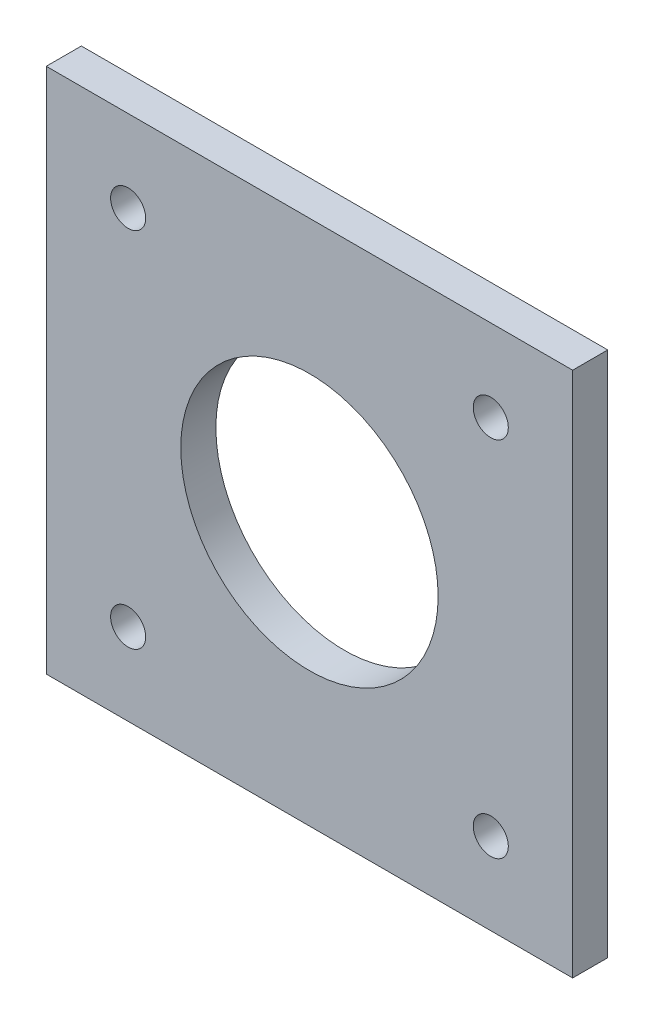
SolidWorks part; units mm, degrees
material "Plain Carbon Steel"
ref_plane "Front Plane" through (0, 0, 0) normal (0, 0, 1) x (1, 0, 0)
ref_plane "Top Plane" through (0, 0, 0) normal (0, 1, 0) x (1, 0, 0)
ref_plane "Right Plane" through (0, 0, 0) normal (1, 0, 0) x (0, 0, -1)
sketch "Sketch1" plane through (0, 0, 0) normal (0, 0, 1) x (1, 0, 0)
  line L0 (16.7358, 20.15) -> (-16.7358, 20.15)
  line L1 (-16.7358, 20.15) -> (-20.15, 16.7358)
  line L2 (-20.15, 16.0771) -> (-20.15, -16.7358)
  line L5 (-16.7358, -20.15) -> (16.7358, -20.15)
  line L7 (20.15, -16.7358) -> (20.15, 16.7358)
  line L8 (20.15, 16.7358) -> (16.7358, 20.15)
  line L9 (-20.15, 16.0771) -> (-20.15, 16.7358)
  line L10 (-20.15, -16.7358) -> (-20.15, -20.15)
  line L11 (-20.15, -20.15) -> (-16.7358, -20.15)
  line L12 (16.7358, -20.15) -> (20.15, -20.15)
  line L13 (20.15, -20.15) -> (20.15, -16.7358)
  line L15 (-22.5, 22.5) -> (22.5, 22.5)
  line L16 (-22.5, 22.5) -> (-22.5, -22.5)
  line L17 (-22.5, -22.5) -> (22.5, -22.5)
  line L18 (22.5, 22.5) -> (22.5, -22.5)
  circle A0 centre (-15.5, 15.5) radius 1.5
  circle A1 centre (-15.5, -15.5) radius 1.5
  circle A2 centre (15.5, 15.5) radius 1.5
  circle A3 centre (15.5, -15.5) radius 1.5
  circle A4 centre (0, 0) radius 11
  dimension "D1" = 22
  dimension "D2" = 3
  dimension "D3" = 3
  dimension "D4" = 3
  dimension "D5" = 3
  dimension "D6" = 45
  dimension "D7" = 45
  dimension "D8" = 22.5
  dimension "D9" = 22.5
extrude "Boss-Extrude1" add sketch "Sketch1" along normal blind 3 contours L18 L15 L16 L17 L13 L12 L5 L11 L10 L2 L9 L1 L0 L8 L7 | L12 L13 L7 L8 L0 L1 L9 L2 L10 L11 L5 A4 A3 A2 A1 A0
sketch "Sketch2" plane through (0, -24.1499, 0) normal (0, 1, 0) x (1, 0, 0)
  line L7 (6.0001, 199.3766) -> (6.0001, -250.6234) construction
  line L8 (5.9984, 199.3766) -> (5.9984, -250.6234) construction
  line L9 (-5.9999, 199.3766) -> (-5.9999, -250.6234) construction
  line L10 (-22.5, -3) -> (-22.5, 0) construction
  line L11 (5.9001, -64) -> (-5.8999, -64)
  line L12 (5.9001, -64) -> (5.9001, 1)
  line L13 (5.9001, 1) -> (-5.8999, 1)
  line L14 (-5.8999, -64) -> (-5.8999, 1)
  line L15 (-22.5, 1) -> (22.5, 1)
  line L16 (-22.5, 1) -> (-22.5, -64)
  line L19 (-19.4999, 0) -> (19.5, 0)
  line L21 (-22.5, -64) -> (22.5, -64)
  line L22 (22.5, 1) -> (22.5, -64)
  line L25 (-22.5, -3) -> (22.5, -3) construction
  line L26 (22.5, -3) -> (22.5, 0) construction
  circle A0 centre (0.0001, -34) radius 2
  circle A1 centre (-0.0016, -59) radius 2
  point P2 (22.5, -1.5)
  dimension "D3" = 4
  dimension "D4" = 4
  dimension "D2" = 35
  dimension "D5" = 25
  dimension "D6" = 0
  dimension "D7" = 6
  dimension "D8" = 6
  dimension "D9" = 0.1
  dimension "D10" = 65
  dimension "D11" = 0.1
  dimension "D12" = 0
  dimension "D13" = 0
  dimension "D14" = 4
  dimension "D15" = 0
